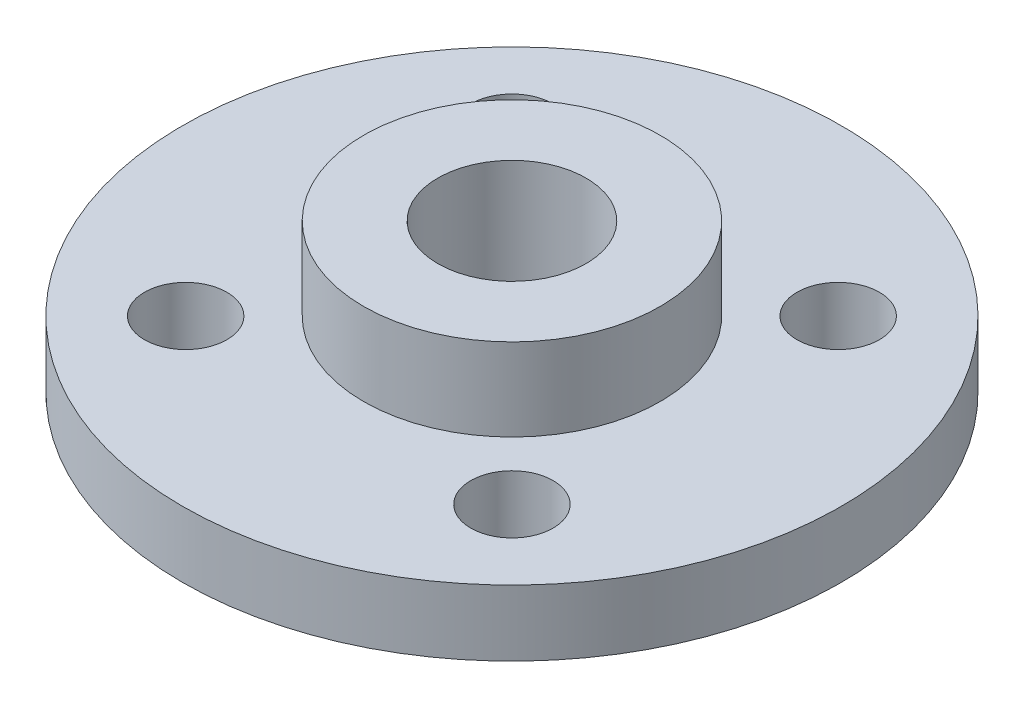
SolidWorks part; units mm, degrees
ref_plane "Front Plane" through (0, 0, 0) normal (0, 0, 1) x (1, 0, 0)
ref_plane "Top Plane" through (0, 0, 0) normal (0, 1, 0) x (1, 0, 0)
ref_plane "Right Plane" through (0, 0, 0) normal (1, 0, 0) x (0, 0, -1)
sketch "Sketch1" plane through (0, 0, 0) normal (0, 1, 0) x (1, 0, 0)
  line L0 (-4.9497, 4.9497) -> (4.9497, 4.9497) construction
  line L1 (4.9497, 4.9497) -> (4.9497, -4.9497) construction
  circle A0 centre (0, 0) radius 10
  circle A1 centre (-4.9497, 4.9497) radius 1.25
  circle A2 centre (4.9497, 4.9497) radius 1.25
  circle A3 centre (4.9497, -4.9497) radius 1.25
  circle A4 centre (-4.9497, -4.9497) radius 1.25
  circle A5 centre (0, 0) radius 7 construction
  circle A6 centre (0, 0) radius 1.5
  dimension "D1" = 20
  dimension "D2" = 2.5
  dimension "D3" = 3
  dimension "D4" = 14
extrude "Boss-Extrude1" add sketch "Sketch1" along normal blind 2
cosmetic thread "Cosmetic Thread1" parameters "D2"=3
cosmetic thread "Cosmetic Thread2" parameters "D2"=3
cosmetic thread "Cosmetic Thread3" parameters "D2"=3
cosmetic thread "Cosmetic Thread4" parameters "D2"=3
sketch "Sketch2" plane through (0, 2, 0) normal (0, 1, 0) x (1, 0, 0)
  circle A0 centre (0, 0) radius 4.5
  circle A1 centre (0, 0) radius 1.5 construction
  circle A2 centre (0, 0) radius 1.5
  dimension "D1" = 9
extrude "Boss-Extrude2" add sketch "Sketch2" along normal blind 2.5
sketch "Sketch3" plane through (0, 4.5, 0) normal (0, 1, 0) x (1, 0, 0)
  circle A0 centre (0, 0) radius 2.25
  dimension "D1" = 4.5
extrude "Cut-Extrude1" cut sketch "Sketch3" against normal blind 3.6
